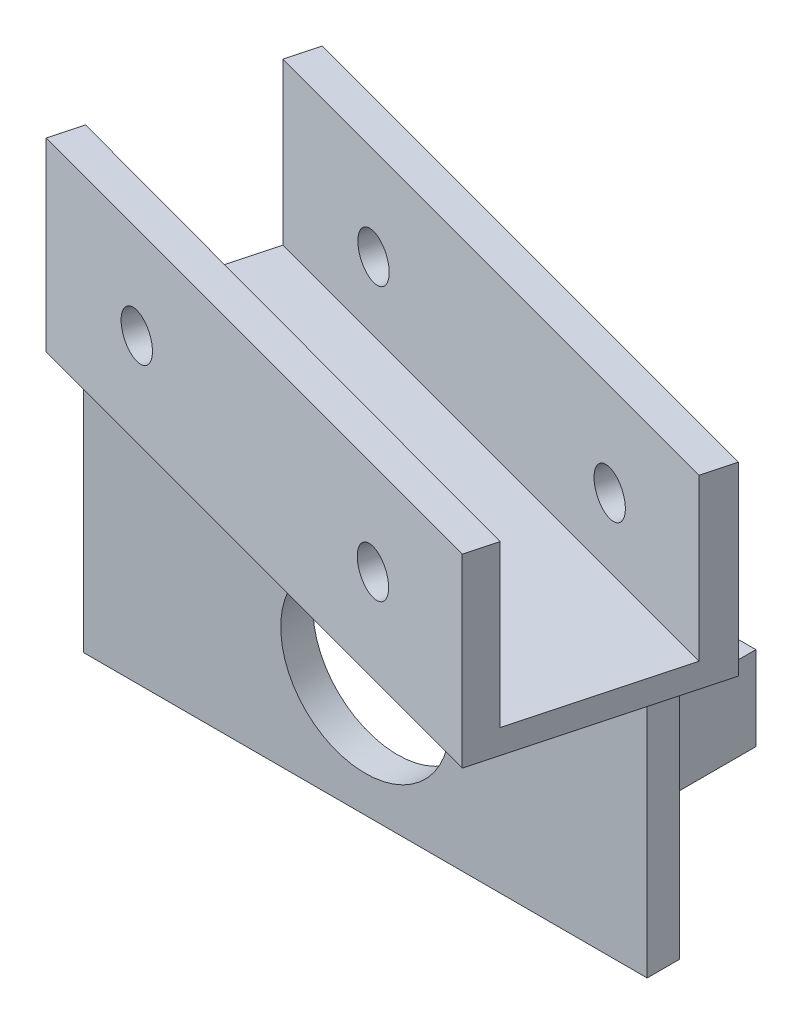
SolidWorks part; units mm, degrees
ref_plane "Front Plane" through (0, 0, 0) normal (0, 0, 1) x (1, 0, 0)
ref_plane "Top Plane" through (0, 0, 0) normal (0, 1, 0) x (1, 0, 0)
ref_plane "Right Plane" through (0, 0, 0) normal (1, 0, 0) x (0, 0, -1)
sketch "Sketch1" plane through (0, 0, 0) normal (0, 0, 1) x (1, 0, 0)
  line L1 (0, 0) -> (70, 0)
  line L2 (0, 0) -> (0, -30)
  line L3 (0, -30) -> (70, -30)
  line L4 (70, 0) -> (70, -30)
  circle A0 centre (35, -15) radius 10.5
  point P7 (70, -15)
  point P8 (35, -30)
  dimension "D1" = 21
  dimension "D2" = 30
  dimension "D3" = 70
extrude "Boss-Extrude1" add sketch "Sketch1" along normal blind 4
sketch "Sketch3" plane through (0, 0, 0) normal (0, 0, -1) x (-1, 0, 0)
  line L0 (-62.5, -8.9384) -> (-54.349, -8.9384)
  line L1 (-54.349, -8.9384) -> (-54.349, -19.3738)
  line L2 (-54.349, -19.3738) -> (-62.5, -19.3738)
  line L3 (-7.5, -5) -> (-14.3209, -5)
  line L4 (-7.5, -25) -> (-7.5, -5)
  line L5 (-62.5, -25) -> (-7.5, -25)
  line L6 (-62.5, -5) -> (-62.5, -25)
  line L7 (-7.5, -5) -> (-62.5, -5)
  line L8 (-7.5, -25) -> (-7.5, -5)
  line L10 (-62.5, -8.9384) -> (-62.5, -19.3738)
  line L12 (-14.3209, -5) -> (-14.3209, -25)
  line L13 (-14.3209, -25) -> (-7.5, -25)
  dimension "D1" = 0
extrude "Boss-Extrude2" add sketch "Sketch3" along normal blind 17
sketch "Sketch4" plane through (0, 0, -17) normal (0, 0, -1) x (-1, 0, 0)
  circle A0 centre (-58.5, -14.2891) radius 1 construction
  circle A1 centre (-58.5, -14.2891) radius 1
  circle A2 centre (-11.5, -7) radius 1 construction
  circle A3 centre (-11.5, -7) radius 1
  circle A4 centre (-11.5, -23) radius 1 construction
  circle A5 centre (-11.5, -23) radius 1
extrude "Cut-Extrude1" cut sketch "Sketch4" against normal blind 17
sketch "Sketch7" plane through (0, 0, 0) normal (0, 1, 0) x (1, 0, 0)
  line L1 (-4.6304, -4) -> (65.9508, -22.9122)
  line L2 (65.9508, -22.9122) -> (73.1977, 4.1338)
  line L5 (-4.6304, -4) -> (2.6166, 23.0459)
  line L8 (70, -4) -> (0, -4) construction
  line L9 (73.1977, 4.1338) -> (2.6166, 23.0459)
  dimension "D1" = 28
  dimension "D2" = 15
extrude "Boss-Extrude4" add sketch "Sketch7" along normal blind 3
sketch "Sketch9" plane through (0, 3, 0) normal (0, 1, 0) x (1, 0, 0)
  line L0 (-4.6304, -4) -> (65.9508, -22.9122)
  line L1 (65.9508, -22.9122) -> (66.944, -19.2056)
  line L2 (65.9508, -22.9122) -> (73.1977, 4.1338) construction
  line L3 (66.944, -19.2056) -> (-3.5951, -0.1363)
  line L4 (2.6166, 23.0459) -> (-4.6304, -4) construction
  line L5 (-3.5951, -0.1363) -> (-4.6304, -4)
  line L6 (2.6166, 23.0459) -> (1.5813, 19.1822)
  line L7 (1.5813, 19.1822) -> (72.1624, 0.2701)
  line L8 (72.1624, 0.2701) -> (73.1977, 4.1338)
  line L9 (73.1977, 4.1338) -> (2.6166, 23.0459)
  dimension "D1" = 4
  dimension "D2" = 4
extrude "Boss-Extrude5" add sketch "Sketch9" along normal blind 20
sketch "Sketch10" plane through (5.9368, 0, -22.1563) normal (0.2588, 0, -0.9659) x (-0.9659, 0, -0.2588)
  line L0 (-69.6337, 23) -> (-69.6337, 0) construction
  circle A0 centre (-53.9537, 11.5) radius 2.75
  circle A1 centre (-12.4883, 11.5) radius 2.75
  point P6 (-69.6337, 11.5)
  dimension "D1" = 5.5
  dimension "D2" = 5.5
extrude "Cut-Extrude2" cut sketch "Sketch10" against normal through all
